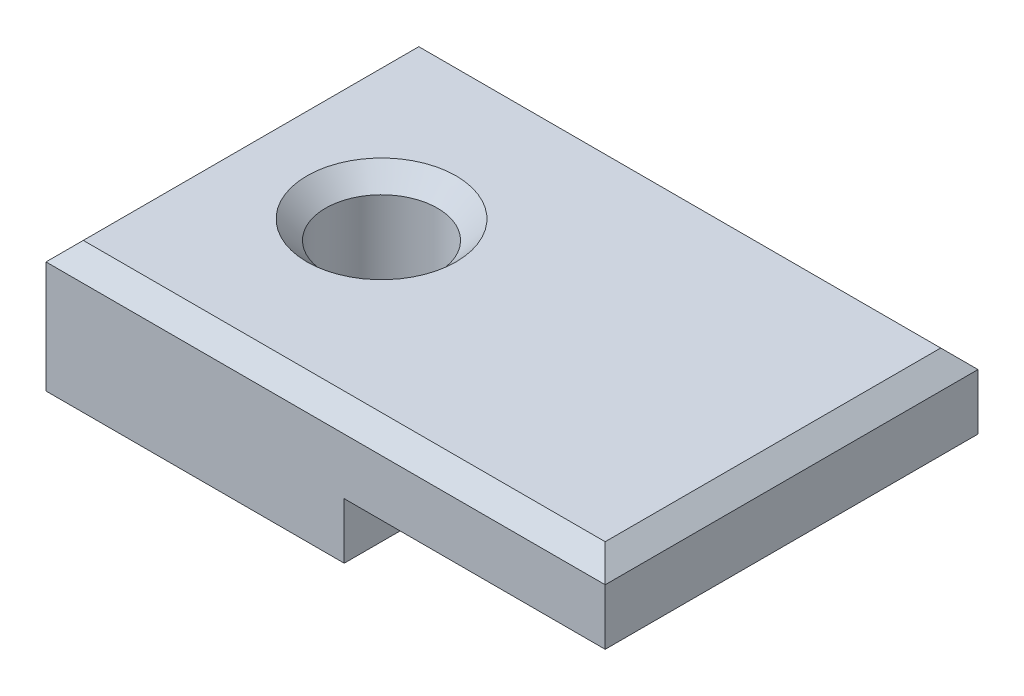
SolidWorks part; units mm, degrees
ref_plane "Front Plane" through (0, 0, 0) normal (0, 0, 1) x (1, 0, 0)
ref_plane "Top Plane" through (0, 0, 0) normal (0, 1, 0) x (1, 0, 0)
ref_plane "Right Plane" through (0, 0, 0) normal (1, 0, 0) x (0, 0, -1)
sketch "Sketch1" plane through (0, 0, 0) normal (0, 1, 0) x (1, 0, 0)
  line L1 (-8, 10) -> (22, 10)
  line L2 (-8, 10) -> (-8, -10)
  line L3 (-8, -10) -> (22, -10)
  line L4 (22, 10) -> (22, -10)
  line L5 (7, -10) -> (7, 10) construction
  line L6 (-8, 0) -> (22, 0) construction
  circle A0 centre (0, 0) radius 3
  point P6 (0, 0)
  point P212 (7, 0)
  dimension "D1" = 6
  dimension "D2" = 20
  dimension "D3" = 8
  dimension "D4" = 30
extrude "Boss-Extrude1" add sketch "Sketch1" along normal blind 7
sketch "Sketch2" plane through (0, 0, 0) normal (0, -1, 0) x (1, 0, 0)
  line L1 (8, 10) -> (-8, 10)
  line L2 (8, 10) -> (8, -10)
  line L3 (8, -10) -> (-8, -10)
  line L4 (-8, 10) -> (-8, -10)
  line L5 (0, -10) -> (0, 10) construction
  line L6 (8, 0) -> (-8, 0) construction
  point P0 (0, 0)
extrude "Cut-Extrude1" cut sketch "Sketch2" against normal blind 3 flip side to cut
chamfer "Chamfer1" distance 1 angle 45 5 edges at (0, 7, 3) (7, 7, -10) (22, 7, 0) (7, 7, 10) (-8, 7, 0)
